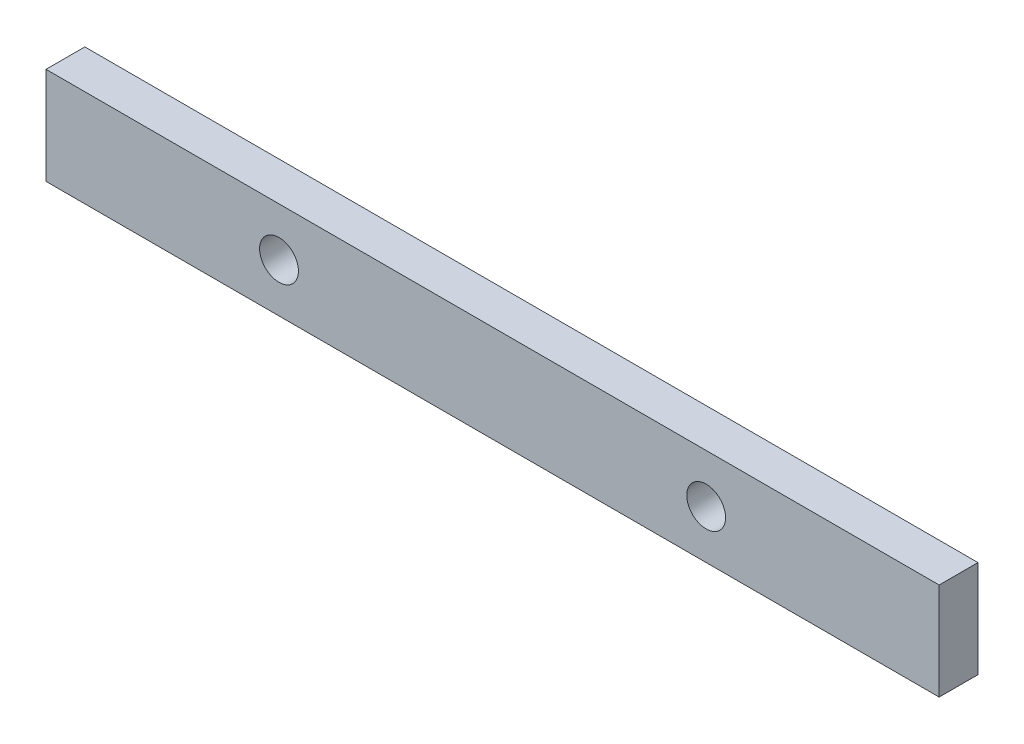
SolidWorks part; units mm, degrees
ref_plane "Front Plane" through (0, 0, 0) normal (0, 0, 1) x (1, 0, 0)
ref_plane "Top Plane" through (0, 0, 0) normal (0, 1, 0) x (1, 0, 0)
ref_plane "Right Plane" through (0, 0, 0) normal (1, 0, 0) x (0, 0, -1)
sketch "Sketch1" plane through (0, 0, 0) normal (0, 0, 1) x (1, 0, 0)
  line L1 (-230, 25) -> (230, 25)
  line L2 (-230, 25) -> (-230, -25)
  line L3 (-230, -25) -> (230, -25)
  line L4 (230, 25) -> (230, -25)
  line L5 (-230, 25) -> (230, -25) construction
  line L6 (-230, -25) -> (230, 25) construction
  circle A0 centre (110, 0) radius 10
  circle A1 centre (-110, 0) radius 10
  point P0 (0, 0)
  dimension "D5" = 20
  dimension "D6" = 20
  dimension "D1" = 50
  dimension "D2" = 460
  dimension "D3" = 110
  dimension "D4" = 110
extrude "Boss-Extrude1" add sketch "Sketch1" along normal blind 20
